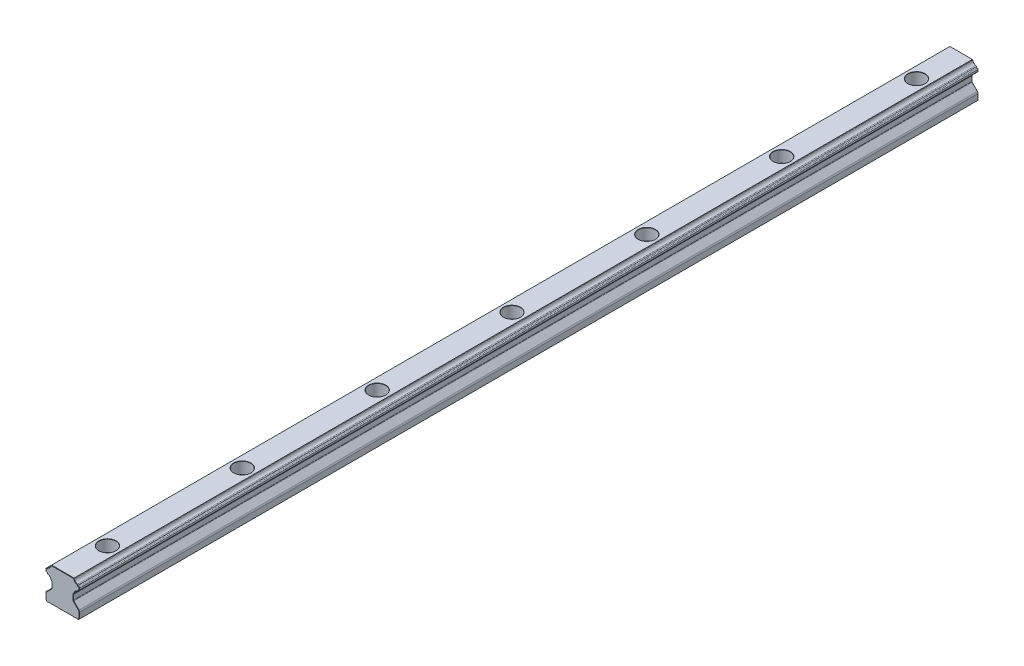
SolidWorks part; units mm, degrees
material "Plain Carbon Steel"
ref_plane "Front Plane" through (0, 0, 0) normal (0, 0, 1) x (1, 0, 0)
ref_plane "Top Plane" through (0, 0, 0) normal (0, 1, 0) x (1, 0, 0)
ref_plane "Right Plane" through (0, 0, 0) normal (1, 0, 0) x (0, 0, -1)
sketch "Rail Profile" plane through (0, 0, 0) normal (0, 0, 1) x (1, 0, 0)
  line L47 (0, 0) -> (0, 20) construction
  line L48 (-7, 0) -> (7, 0)
  line L49 (7, 0) -> (7.5, 0.5)
  line L50 (7.5, 0.5) -> (7.5, 3.0858)
  line L58 (7.2071, 3.7929) -> (4.8672, 6.1328)
  line L59 (4.75, 6.4157) -> (4.75, 8.5843)
  line L60 (4.8672, 8.8672) -> (5.063, 9.063)
  line L61 (7.5, 11.6657) -> (7.5, 12.3343)
  line L62 (-7, 0) -> (-7.5, 0.5)
  line L63 (5, 15) -> (-5, 15)
  line L64 (6.75, 9) -> (6.75, 15) construction
  line L65 (5.063, 14.937) -> (5, 15)
  line L66 (-7.5, 0.5) -> (-7.5, 3.0858)
  line L67 (6.75, 15) -> (3.75, 12) construction
  line L68 (3.75, 12) -> (6.75, 9) construction
  line L69 (7.1, 12.3343) -> (7.1, 11.6657) construction
  line L70 (6.4042, 13.0301) -> (6.4042, 10.9699) construction
  line L71 (-7.2071, 3.7929) -> (-4.8672, 6.1328)
  line L72 (-4.75, 6.4157) -> (-4.75, 8.5843)
  line L73 (-4.8672, 8.8672) -> (-5.063, 9.063)
  line L74 (5, 15) -> (8, 12) construction
  line L75 (4.8672, 8.8672) -> (8, 12) construction
  line L76 (-7.5, 11.6657) -> (-7.5, 12.3343)
  line L77 (-5.063, 14.937) -> (-5, 15)
  arc A4 (6.4734, 13.4241) -> (5.1741, 14.7234) centre (6.75, 15) cw
  arc A6 (5.1741, 9.2766) -> (6.4734, 10.5759) centre (6.75, 9) cw
  arc A7 (7.2071, 3.7929) -> (7.5, 3.0858) centre (6.5, 3.0858) cw
  arc A8 (5.063, 14.937) -> (5.1741, 14.7234) centre (4.7801, 14.6542) cw
  arc A9 (6.4734, 13.4241) -> (6.8012, 13.0792) centre (6.4042, 13.0301) cw
  arc A10 (7.1491, 12.7313) -> (7.5, 12.3343) centre (7.1, 12.3343) cw
  arc A11 (7.5, 11.6657) -> (7.1491, 11.2687) centre (7.1, 11.6657) cw
  arc A12 (6.8012, 10.9208) -> (6.4734, 10.5759) centre (6.4042, 10.9699) cw
  arc A13 (5.1741, 9.2766) -> (5.063, 9.063) centre (4.7801, 9.3458) cw
  arc A14 (4.8672, 8.8672) -> (4.75, 8.5843) centre (5.15, 8.5843) ccw
  arc A15 (4.75, 6.4157) -> (4.8672, 6.1328) centre (5.15, 6.4157) ccw
  arc A16 (6.8012, 13.0792) -> (7.1491, 12.7313) centre (7.1981, 13.1283) ccw
  arc A17 (7.1491, 11.2687) -> (6.8012, 10.9208) centre (7.1981, 10.8717) ccw
  arc A18 (-7.2071, 3.7929) -> (-7.5, 3.0858) centre (-6.5, 3.0858) ccw
  arc A19 (-4.75, 6.4157) -> (-4.8672, 6.1328) centre (-5.15, 6.4157) cw
  arc A20 (-4.8672, 8.8672) -> (-4.75, 8.5843) centre (-5.15, 8.5843) cw
  arc A21 (-5.1741, 9.2766) -> (-5.063, 9.063) centre (-4.7801, 9.3458) ccw
  arc A22 (-5.1741, 9.2766) -> (-6.4734, 10.5759) centre (-6.75, 9) ccw
  arc A23 (-6.8012, 10.9208) -> (-6.4734, 10.5759) centre (-6.4042, 10.9699) ccw
  arc A24 (-7.1491, 11.2687) -> (-6.8012, 10.9208) centre (-7.1981, 10.8717) cw
  arc A25 (-7.5, 11.6657) -> (-7.1491, 11.2687) centre (-7.1, 11.6657) ccw
  arc A26 (-7.1491, 12.7313) -> (-7.5, 12.3343) centre (-7.1, 12.3343) ccw
  arc A27 (-6.8012, 13.0792) -> (-7.1491, 12.7313) centre (-7.1981, 13.1283) cw
  arc A28 (-6.4734, 13.4241) -> (-6.8012, 13.0792) centre (-6.4042, 13.0301) ccw
  arc A29 (-6.4734, 13.4241) -> (-5.1741, 14.7234) centre (-6.75, 15) ccw
  arc A30 (-5.063, 14.937) -> (-5.1741, 14.7234) centre (-4.7801, 14.6542) ccw
  point P2 (4.75, 7.5)
  point P12 (7.5, 12)
  point P19 (6.75, 12)
  point P25 (5.1578, 14.8422)
  point P50 (8, 12)
  point P78 (0, 15)
  dimension "Rb" = 1.6
  dimension "Rf1" = 1
  dimension "Rf2" = 0.4
  dimension "WR" = 15
  dimension "Wi" = 9.5
  dimension "Wt" = 5
  dimension "Ac" = 135
  dimension "HR" = 15
  dimension "Hm" = 7.5
  dimension "Hb" = 12
  dimension "Hc" = 0.5
  dimension "Wb" = 7.5
extrude "Body" add sketch "Rail Profile" against normal blind 400
chamfer "Aesthetic Chamfer" distance 0.15 angle 45 84 edges at (-5.0315, 14.9685, 0) (-5.135, 14.8388, 0) (-5.6186, 13.8686, 0) (-6.6941, 13.3057, 0) (-6.9153, 12.8454, 0) (-7.3997, 12.5992, 0) (-7.5, 12, 0) (-7.3997, 11.4008, 0) (-6.9153, 11.1546, 0) (-6.6941, 10.6943, 0) (-5.6186, 10.1314, 0) (-5.135, 9.1612, 0) (-4.9651, 8.9651, 0) (-4.7804, 8.7374, 0) (-4.75, 7.5, 0) (-4.7804, 6.2626, 0) (-6.0371, 4.9629, 0) (-7.4239, 3.4685, 0) (-7.5, 1.7929, 0) (-7.25, 0.25, 0) (0, 0, 0) (7.25, 0.25, 0) (5.0315, 14.9685, 0) (5.135, 14.8388, 0) (5.6186, 13.8686, 0) (6.6941, 13.3057, 0) (6.9153, 12.8454, 0) (7.3997, 12.5992, 0) (7.5, 12, 0) (7.3997, 11.4008, 0) (6.9153, 11.1546, 0) (6.6941, 10.6943, 0) (5.6186, 10.1314, 0) (5.135, 9.1612, 0) (4.9651, 8.9651, 0) (4.7804, 8.7374, 0) (7.5, 1.7929, 0) (4.75, 7.5, 0) (7.4239, 3.4685, 0) (4.7804, 6.2626, 0) (6.0371, 4.9629, 0) (0, 15, 0) (5.0315, 14.9685, -400) (5.135, 14.8388, -400) (5.6186, 13.8686, -400) (6.6941, 13.3057, -400) (6.9153, 12.8454, -400) (7.3997, 12.5992, -400) (7.5, 12, -400) (7.3997, 11.4008, -400) (6.9153, 11.1546, -400) (6.6941, 10.6943, -400) (5.6186, 10.1314, -400) (5.135, 9.1612, -400) (4.9651, 8.9651, -400) (4.7804, 8.7374, -400) (4.75, 7.5, -400) (4.7804, 6.2626, -400) (6.0371, 4.9629, -400) (7.4239, 3.4685, -400) (7.5, 1.7929, -400) (7.25, 0.25, -400) (0, 0, -400) (-7.25, 0.25, -400) (-5.0315, 14.9685, -400) (-5.135, 14.8388, -400) (-5.6186, 13.8686, -400) (-6.6941, 13.3057, -400) (-6.9153, 12.8454, -400) (-7.3997, 12.5992, -400) (-7.5, 12, -400) (-7.3997, 11.4008, -400) (-6.9153, 11.1546, -400) (-6.6941, 10.6943, -400) (-5.6186, 10.1314, -400) (-7.5, 1.7929, -400) (-5.135, 9.1612, -400) (-7.4239, 3.4685, -400) (-4.9651, 8.9651, -400) (-6.0371, 4.9629, -400) (-4.7804, 8.7374, -400) (-4.7804, 6.2626, -400) (-4.75, 7.5, -400) (0, 15, -400)
hole_wizard "Mounting Hole" positions "3DSketch1" profile "Sketch1" counterbore size "M4" standard "ISO" end condition through all
sketch3d "3DSketch1"
  point P0 (0, 15, -20)
  dimension "D1" = 7.5
  dimension "E1" = 20
sketch "Sketch1" plane through (0, 15, -20) normal (1, 0, 0) x (0, 0, 1)
  line L0 (0, 0) -> (0, 15)
  line L1 (2.25, 14.9) -> (2.35, 15)
  line L2 (2.25, 14.9) -> (2.25, 5.4)
  line L3 (2.25, 5.4) -> (2.35, 5.3)
  line L4 (2.35, 5.3) -> (3.75, 5.3)
  line L5 (3.75, 5.3) -> (3.75, 0.1)
  line L6 (3.75, 0.1) -> (3.85, 0)
  line L7 (3.85, 0) -> (0, 0)
  line L8 (-3.75, 0.1) -> (-3.85, 0) construction
  line L9 (-2.25, 5.4) -> (-2.35, 5.3) construction
  line L11 (0, -6.35) -> (0, 107.95) construction
  line L12 (2.35, 15) -> (0, 15)
  line L13 (-2.25, 14.9) -> (-2.35, 15) construction
  dimension "Thru Hole Dia." = 4.5
  dimension "Thru Hole Depth" = 15
  dimension "C'Bore Dia." = 7.5
  dimension "C'Bore Depth" = 5.3
  dimension "Near C'Sink Dia." = 7.7
  dimension "Near C'Sink Angle" = 90
  dimension "Mid C'Sink Dia." = 4.7
  dimension "Mid C'Sink Angle" = 90
  dimension "Far C'Sink Dia." = 4.7
  dimension "Far C'Sink Angle" = 90
fillet "Production Fillet" radius 0.1 1 edges at (0, 9.7, -16.25)
pattern_linear "Mounting Holes Pattern" count 7 spacing 60 along (0, 0, -1) of "Mounting Hole", "Production Fillet"
equation "\"Wt@Rail Profile\"= \"WR@Rail Profile\" / 3'Top Side Half Width"
equation "\"Hm@Rail Profile\"= \"HR@Rail Profile\" / 2'Recirculation Avoidance Height"
equation "\"Hb@Rail Profile\"= 0.8 * \"HR@Rail Profile\"'Pivot Height"
equation "\"Hc@Rail Profile\"= \"WR@Rail Profile\" / 30'Chamfer Width"
equation "\"Wb@Rail Profile\"= \"WR@Rail Profile\" / 2'Ball Center Cross Width"
equation "\"D1@3DSketch1\"= \"WR@Rail Profile\" / 2'Hole Center Position"
